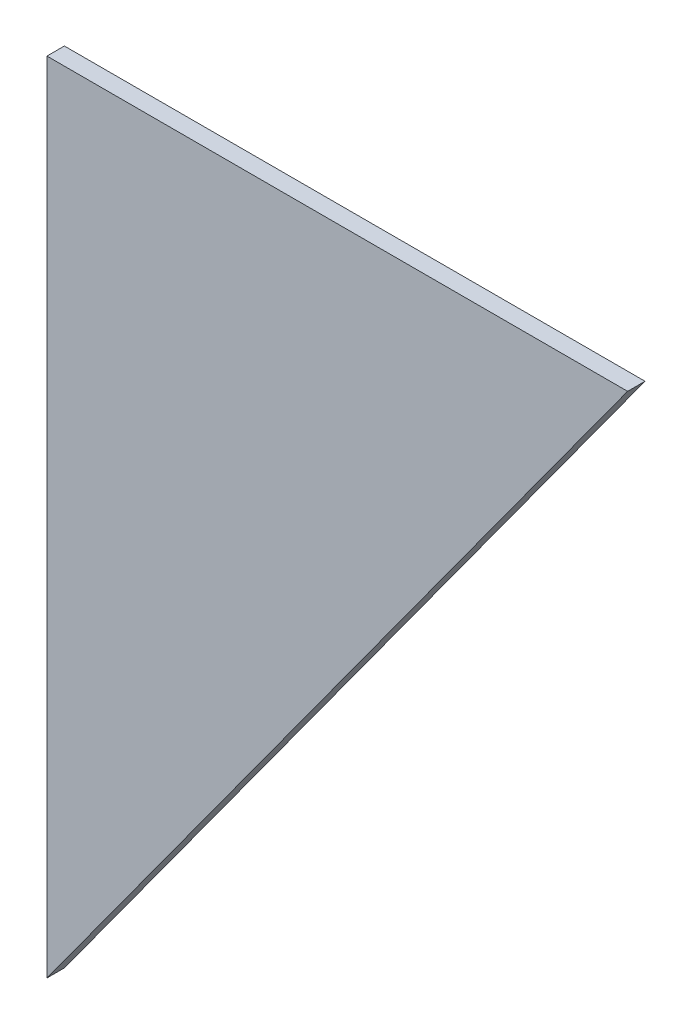
SolidWorks part; units mm, degrees
material "6061 Alloy"
ref_plane "Front Plane" through (0, 0, 0) normal (0, 0, 1) x (1, 0, 0)
ref_plane "Top Plane" through (0, 0, 0) normal (0, 1, 0) x (1, 0, 0)
ref_plane "Right Plane" through (0, 0, 0) normal (1, 0, 0) x (0, 0, -1)
sketch "Sketch1" plane through (0, 0, 0) normal (0, 0, 1) x (1, 0, 0)
  line L0 (0, 0) -> (0, 139.7)
  line L1 (0, 139.7) -> (101.6, 139.7)
  line L2 (101.6, 139.7) -> (0, 0)
  dimension "D1" = 101.6
  dimension "D2" = 139.7
extrude "Boss-Extrude1" add sketch "Sketch1" along normal blind 3.048
equation "\"base length\" = 21"
equation "\"glass pane length\" = 14.125"
equation "\"glass pane width\" = 10.1875"
equation "\"glass pane wall width\" = 3/4"
equation "\"glass lip\" = 1/4"
equation "\"bolt diameter\" = 0.2"
equation "\"stepper body width\" = 2.22"
equation "\"stepper mount offset\" = 0.19"
equation "\"stepper mount diameter\" = 0.19"
equation "\"stepper shaft offset from body\" = 0.79"
equation "\"stepper spacer thickness\" = 0.2"
equation "\"y axis stepper wall height off base\" = 8"
equation "\"y axis stepper wall bracket thickness\" = 1"
equation "\"y axis stepper wall mount side offset\" = 1/2"
equation "\"y axis stepper wall mount top offset\" = 1/2"
equation "\"y axis stepper wall width\" = \"stepper body width\" + 1                  "
equation "\"y axis bracket height to hole\"= 3.5"
equation "\"thin metal\" = 0.12"
equation "\"thick metal\" = 0.25"
equation "\"foot diameter\"= 0.2"
equation "\"foot inset from corner\"= 1"
equation "\"recognizer width\" = 2.5"
equation "\"recognizer nut plate height\" = 1.25"
equation "\"recognizer nut plate offset\" = 1.5"
equation "\"recognizer arm length\"= 7"
equation "\"recognizer bracket length\" = 4"
equation "\"D1@Boss-Extrude1\" = \"thin metal\""
